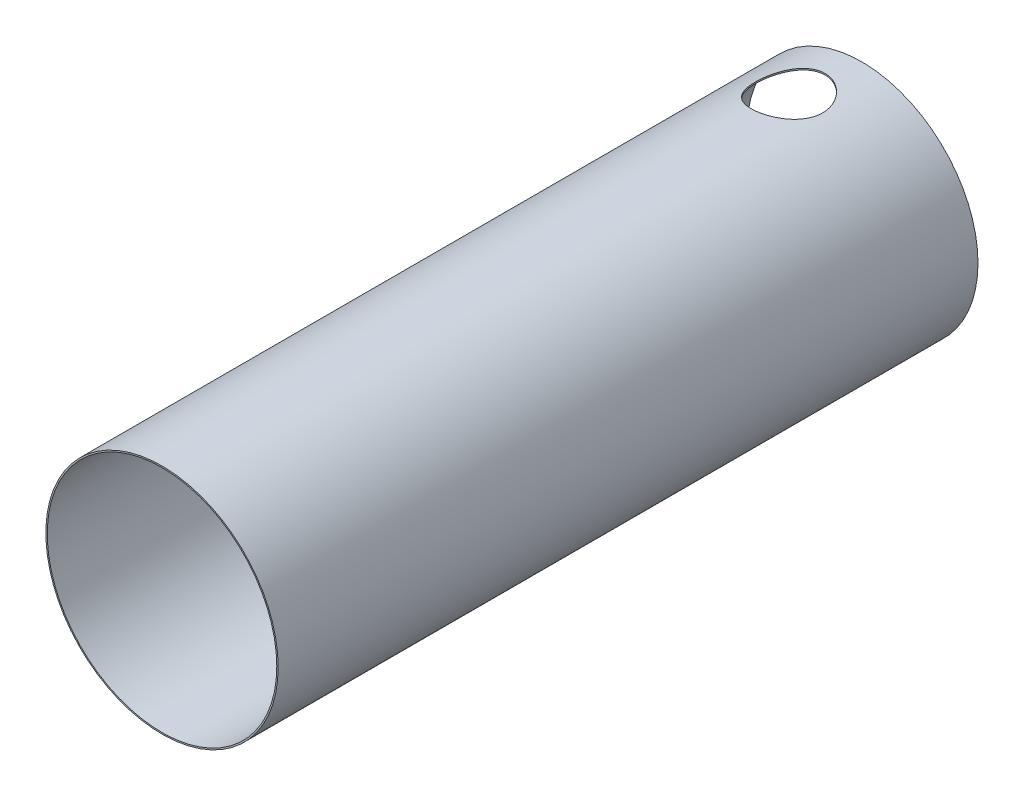
SolidWorks part; units mm, degrees
ref_plane "Front Plane" through (0, 0, 0) normal (0, 0, 1) x (1, 0, 0)
ref_plane "Top Plane" through (0, 0, 0) normal (0, 1, 0) x (1, 0, 0)
ref_plane "Right Plane" through (0, 0, 0) normal (1, 0, 0) x (0, 0, -1)
sketch "Sketch1" plane through (0, 0, 0) normal (0, 0, 1) x (1, 0, 0)
  circle A0 centre (0, 0) radius 20.5
  circle A1 centre (0, 0) radius 20.75
  dimension "D1" = 41
  dimension "D2" = 41.5
extrude "Extrude1" add sketch "Sketch1" along normal blind 125
sketch "Sketch2" plane through (0, 0, 0) normal (0, 1, 0) x (1, 0, 0)
  circle A0 centre (-2, -11) radius 6
  dimension "D1" = 12
  dimension "D2" = 11
  dimension "D3" = 2
extrude "Cut-Extrude1" cut sketch "Sketch2" along normal through all
